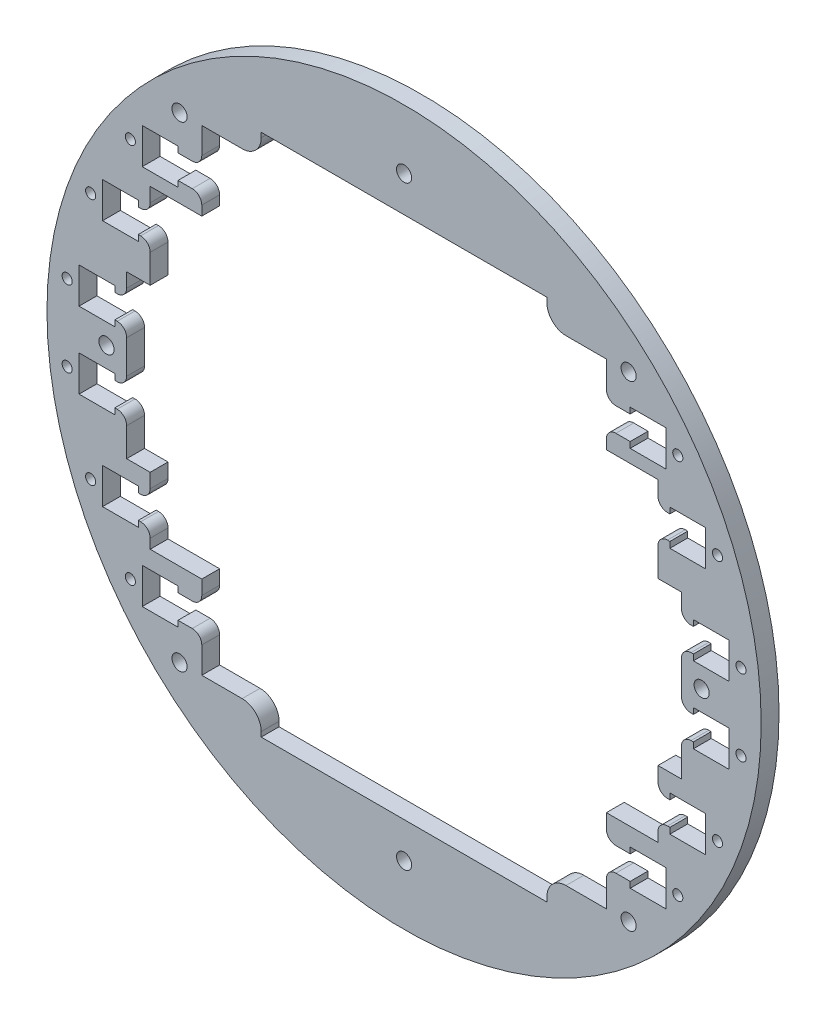
SolidWorks part; units mm, degrees
material "Delrin 2700 NC010, Low Viscosity Acetal Copolymer (SS)"
ref_plane "Front Plane" through (0, 0, 0) normal (0, 0, 1) x (1, 0, 0)
ref_plane "Top Plane" through (0, 0, 0) normal (0, 1, 0) x (1, 0, 0)
ref_plane "Right Plane" through (0, 0, 0) normal (1, 0, 0) x (0, 0, -1)
sketch "Sketch1" plane through (0, 0, 0) normal (0, 0, 1) x (1, 0, 0)
  circle A0 centre (0, 0) radius 95.25
  dimension "D1" = 190.5
extrude "Boss-Extrude1" add sketch "Sketch1" along normal blind 4.7625
sketch "Sketch11" plane through (0, 0, 4.7625) normal (0, 0, 1) x (1, 0, 0)
  line L0 (-69.8306, 55.5625) -> (-69.8306, 46.0375)
  line L1 (-69.8306, 46.0375) -> (-60.3056, 46.0375)
  line L2 (-60.3056, 46.0375) -> (-60.3056, 47.625)
  line L3 (-60.3056, 47.625) -> (-68.2431, 47.625)
  line L4 (-68.2431, 47.625) -> (-68.2431, 53.975)
  line L5 (-68.2431, 53.975) -> (-60.3056, 53.975)
  line L6 (-60.3056, 53.975) -> (-60.3056, 55.5625)
  line L7 (-60.3056, 55.5625) -> (-69.8306, 55.5625)
  line L8 (-69.8306, 50.8) -> (-65.0681, 50.8) construction
  line L9 (-86.6849, 14.9225) -> (-86.6849, 5.3975)
  line L10 (-86.6849, 5.3975) -> (-77.1599, 5.3975)
  line L11 (-77.1599, 5.3975) -> (-77.1599, 6.985)
  line L12 (-77.1599, 6.985) -> (-85.0974, 6.985)
  line L13 (-85.0974, 6.985) -> (-85.0974, 13.335)
  line L14 (-85.0974, 13.335) -> (-77.1599, 13.335)
  line L15 (-77.1599, 13.335) -> (-77.1599, 14.9225)
  line L16 (-77.1599, 14.9225) -> (-86.6849, 14.9225)
  line L17 (-80.4208, 37.7825) -> (-80.4208, 28.2575)
  line L18 (-80.4208, 28.2575) -> (-70.8958, 28.2575)
  line L19 (-70.8958, 28.2575) -> (-70.8958, 29.845)
  line L20 (-70.8958, 29.845) -> (-78.8333, 29.845)
  line L21 (-78.8333, 29.845) -> (-78.8333, 36.195)
  line L22 (-78.8333, 36.195) -> (-70.8958, 36.195)
  line L23 (-70.8958, 36.195) -> (-70.8958, 37.7825)
  line L24 (-70.8958, 37.7825) -> (-80.4208, 37.7825)
  line L25 (-80.4208, 33.02) -> (-75.6583, 33.02) construction
  line L26 (-86.6849, 10.16) -> (-81.9224, 10.16) construction
  line L27 (0, 0) -> (63.3649, 0) construction
  line L28 (-77.1599, -13.335) -> (-77.1599, -14.9225)
  line L29 (-77.1599, -14.9225) -> (-86.6849, -14.9225)
  line L30 (-85.0974, -13.335) -> (-77.1599, -13.335)
  line L31 (-86.6849, -14.9225) -> (-86.6849, -5.3975)
  line L32 (-85.0974, -6.985) -> (-85.0974, -13.335)
  line L33 (-77.1599, -6.985) -> (-85.0974, -6.985)
  line L34 (-77.1599, -5.3975) -> (-77.1599, -6.985)
  line L35 (-86.6849, -5.3975) -> (-77.1599, -5.3975)
  line L36 (-80.4208, -28.2575) -> (-70.8958, -28.2575)
  line L37 (-70.8958, -28.2575) -> (-70.8958, -29.845)
  line L38 (-70.8958, -29.845) -> (-78.8333, -29.845)
  line L39 (-80.4208, -37.7825) -> (-80.4208, -28.2575)
  line L40 (-78.8333, -29.845) -> (-78.8333, -36.195)
  line L41 (-70.8958, -37.7825) -> (-80.4208, -37.7825)
  line L42 (-78.8333, -36.195) -> (-70.8958, -36.195)
  line L43 (-70.8958, -36.195) -> (-70.8958, -37.7825)
  line L44 (-60.3056, -46.0375) -> (-60.3056, -47.625)
  line L45 (-60.3056, -47.625) -> (-68.2431, -47.625)
  line L46 (-69.8306, -46.0375) -> (-60.3056, -46.0375)
  line L47 (-69.8306, -55.5625) -> (-69.8306, -46.0375)
  line L48 (-68.2431, -47.625) -> (-68.2431, -53.975)
  line L49 (-68.2431, -53.975) -> (-60.3056, -53.975)
  line L50 (-60.3056, -55.5625) -> (-69.8306, -55.5625)
  line L51 (-60.3056, -53.975) -> (-60.3056, -55.5625)
  line L52 (0, 0) -> (0, 41.3514) construction
  line L53 (86.6849, 10.16) -> (81.9224, 10.16) construction
  line L54 (80.4208, 33.02) -> (75.6583, 33.02) construction
  line L55 (69.8306, 50.8) -> (65.0681, 50.8) construction
  line L56 (60.3056, -53.975) -> (60.3056, -55.5625)
  line L57 (60.3056, -55.5625) -> (69.8306, -55.5625)
  line L58 (68.2431, -53.975) -> (60.3056, -53.975)
  line L59 (68.2431, -47.625) -> (68.2431, -53.975)
  line L60 (69.8306, -55.5625) -> (69.8306, -46.0375)
  line L61 (69.8306, -46.0375) -> (60.3056, -46.0375)
  line L62 (60.3056, -47.625) -> (68.2431, -47.625)
  line L63 (60.3056, -46.0375) -> (60.3056, -47.625)
  line L64 (70.8958, -36.195) -> (70.8958, -37.7825)
  line L65 (78.8333, -36.195) -> (70.8958, -36.195)
  line L66 (70.8958, -37.7825) -> (80.4208, -37.7825)
  line L67 (78.8333, -29.845) -> (78.8333, -36.195)
  line L68 (80.4208, -37.7825) -> (80.4208, -28.2575)
  line L69 (70.8958, -29.845) -> (78.8333, -29.845)
  line L70 (70.8958, -28.2575) -> (70.8958, -29.845)
  line L71 (80.4208, -28.2575) -> (70.8958, -28.2575)
  line L72 (86.6849, -5.3975) -> (77.1599, -5.3975)
  line L73 (77.1599, -5.3975) -> (77.1599, -6.985)
  line L74 (77.1599, -6.985) -> (85.0974, -6.985)
  line L75 (85.0974, -6.985) -> (85.0974, -13.335)
  line L76 (86.6849, -14.9225) -> (86.6849, -5.3975)
  line L77 (85.0974, -13.335) -> (77.1599, -13.335)
  line L78 (77.1599, -14.9225) -> (86.6849, -14.9225)
  line L79 (77.1599, -13.335) -> (77.1599, -14.9225)
  line L80 (70.8958, 37.7825) -> (80.4208, 37.7825)
  line L81 (70.8958, 36.195) -> (70.8958, 37.7825)
  line L82 (78.8333, 36.195) -> (70.8958, 36.195)
  line L83 (78.8333, 29.845) -> (78.8333, 36.195)
  line L84 (70.8958, 29.845) -> (78.8333, 29.845)
  line L85 (70.8958, 28.2575) -> (70.8958, 29.845)
  line L86 (80.4208, 28.2575) -> (70.8958, 28.2575)
  line L87 (80.4208, 37.7825) -> (80.4208, 28.2575)
  line L88 (77.1599, 14.9225) -> (86.6849, 14.9225)
  line L89 (77.1599, 13.335) -> (77.1599, 14.9225)
  line L90 (85.0974, 13.335) -> (77.1599, 13.335)
  line L91 (85.0974, 6.985) -> (85.0974, 13.335)
  line L92 (77.1599, 6.985) -> (85.0974, 6.985)
  line L93 (77.1599, 5.3975) -> (77.1599, 6.985)
  line L94 (86.6849, 5.3975) -> (77.1599, 5.3975)
  line L95 (86.6849, 14.9225) -> (86.6849, 5.3975)
  line L96 (60.3056, 55.5625) -> (69.8306, 55.5625)
  line L97 (60.3056, 53.975) -> (60.3056, 55.5625)
  line L98 (68.2431, 53.975) -> (60.3056, 53.975)
  line L99 (68.2431, 47.625) -> (68.2431, 53.975)
  line L100 (60.3056, 47.625) -> (68.2431, 47.625)
  line L101 (60.3056, 46.0375) -> (60.3056, 47.625)
  line L102 (69.8306, 46.0375) -> (60.3056, 46.0375)
  line L103 (69.8306, 55.5625) -> (69.8306, 46.0375)
  circle A0 centre (0, 0) radius 82.55 construction
  point P14 (-65.0681, 55.5625)
  point P23 (-81.9224, 14.9225)
  point P32 (-75.6583, 37.7825)
  dimension "D1" = 165.1
  dimension "D2" = 9.525
  dimension "D3" = 9.525
  dimension "D4" = 1.5875
  dimension "D5" = 1.5875
  dimension "D6" = 1.5875
  dimension "D7" = 50.8
  dimension "D8" = 9.525
  dimension "D9" = 9.525
  dimension "D10" = 1.5875
  dimension "D11" = 1.5875
  dimension "D12" = 33.02
  dimension "D13" = 1.5875
  dimension "D14" = 9.525
  dimension "D15" = 9.525
  dimension "D16" = 1.5875
  dimension "D17" = 1.5875
  dimension "D18" = 1.5875
  dimension "D19" = 10.16
extrude "Cut-Extrude1" cut sketch "Sketch11" against normal through all
sketch "Sketch12" plane through (0, 0, 4.7625) normal (0, 0, 1) x (1, 0, 0)
  line L1 (-68.2431, 53.975) -> (68.2431, 53.975)
  line L2 (-68.2431, 53.975) -> (-68.2431, 47.625)
  line L3 (-68.2431, 47.625) -> (68.2431, 47.625)
  line L4 (68.2431, 53.975) -> (68.2431, 47.625)
  line L5 (-78.8333, 36.195) -> (78.8333, 36.195)
  line L6 (-78.8333, 36.195) -> (-78.8333, 29.845)
  line L7 (-78.8333, 29.845) -> (78.8333, 29.845)
  line L8 (78.8333, 36.195) -> (78.8333, 29.845)
  line L9 (-85.0974, 13.335) -> (85.0974, 13.335)
  line L10 (-85.0974, 13.335) -> (-85.0974, 6.985)
  line L11 (-85.0974, 6.985) -> (85.0974, 6.985)
  line L12 (85.0974, 13.335) -> (85.0974, 6.985)
  line L13 (-85.0974, -6.985) -> (85.0974, -6.985)
  line L14 (-85.0974, -6.985) -> (-85.0974, -13.335)
  line L15 (-85.0974, -13.335) -> (85.0974, -13.335)
  line L16 (85.0974, -6.985) -> (85.0974, -13.335)
  line L17 (-78.8333, -29.845) -> (78.8333, -29.845)
  line L18 (-78.8333, -29.845) -> (-78.8333, -36.195)
  line L19 (-78.8333, -36.195) -> (78.8333, -36.195)
  line L20 (78.8333, -29.845) -> (78.8333, -36.195)
  line L21 (-68.2431, -47.625) -> (68.2431, -47.625)
  line L22 (-68.2431, -47.625) -> (-68.2431, -53.975)
  line L23 (-68.2431, -53.975) -> (68.2431, -53.975)
  line L24 (68.2431, -47.625) -> (68.2431, -53.975)
extrude "Cut-Extrude2" cut sketch "Sketch12" against normal through all
sketch "Sketch13" plane through (0, 0, 4.7625) normal (0, 0, 1) x (1, 0, 0)
  line L0 (60.3056, 53.975) -> (-60.3056, 53.975) construction
  line L1 (53.9556, -63.5) -> (-53.9556, -63.5)
  line L2 (53.9556, -63.5) -> (53.9556, -41.275)
  line L3 (53.9556, 63.5) -> (-53.9556, 63.5)
  line L4 (-53.9556, -63.5) -> (-53.9556, -41.275)
  line L5 (53.9556, -63.5) -> (-53.9556, 63.5) construction
  line L6 (53.9556, 63.5) -> (-53.9556, -63.5) construction
  line L7 (-53.9556, 42.545) -> (-67.7208, 42.545)
  line L8 (-67.7208, -23.495) -> (-67.7208, -41.275)
  line L9 (-53.9556, -41.275) -> (-67.7208, -41.275)
  line L10 (-67.7208, 42.545) -> (-67.7208, 19.685)
  line L11 (-67.7208, 19.685) -> (-73.9849, 19.685)
  line L12 (0, 0) -> (0, 113.4572) construction
  line L13 (-67.7208, -23.495) -> (-73.9849, -23.495)
  line L14 (-73.9849, 19.685) -> (-73.9849, -23.495)
  line L15 (-60.3056, 53.975) -> (-60.3056, 55.5625) construction
  line L16 (-70.8958, 36.195) -> (-70.8958, 37.7825) construction
  line L17 (70.8958, 36.195) -> (-70.8958, 36.195) construction
  line L18 (77.1599, 13.335) -> (-77.1599, 13.335) construction
  line L19 (70.8958, -29.845) -> (-70.8958, -29.845) construction
  line L20 (-77.1599, 13.335) -> (-77.1599, 14.9225) construction
  line L21 (60.3056, -47.625) -> (-60.3056, -47.625) construction
  line L22 (-53.9556, 42.545) -> (-53.9556, 63.5)
  line L23 (53.9556, -41.275) -> (67.7208, -41.275)
  line L24 (53.9556, -63.5) -> (53.9556, -41.275)
  line L25 (67.7208, -23.495) -> (67.7208, -41.275)
  line L26 (67.7208, -23.495) -> (73.9849, -23.495)
  line L27 (73.9849, 19.685) -> (73.9849, -23.495)
  line L28 (67.7208, 19.685) -> (73.9849, 19.685)
  line L29 (67.7208, 42.545) -> (67.7208, 19.685)
  line L30 (53.9556, 42.545) -> (67.7208, 42.545)
  line L31 (53.9556, 42.545) -> (53.9556, 63.5)
  line L32 (53.9556, 42.545) -> (53.9556, 63.5)
  point P0 (0, 0)
  dimension "D1" = 9.525
  dimension "D2" = 6.35
  dimension "D3" = 3.175
  dimension "D4" = 6.35
  dimension "D5" = 6.35
  dimension "D6" = 6.35
  dimension "D7" = 3.175
  dimension "D8" = 6.35
extrude "Cut-Extrude3" cut sketch "Sketch13" against normal through all contours L30 L31 L3 L22 L7 L10 L11 L14 L13 L8 L9 L4 L1 L2 L23 L25 L26 L27 L28 L29
hole_wizard "#10-32 Tapped Hole1" positions "Sketch10" profile "Sketch9" tap size "#10-32" standard "ANSI Inch"
sketch "Sketch10" plane through (0, 0, 4.7625) normal (0, 0, 1) x (1, 0, 0)
  line L0 (-59.8919, 63.5) -> (59.8919, 63.5) construction
  point P0 (-59.8919, 63.5)
  point P2 (59.8919, 63.5)
  point P9 (0, 63.5)
  dimension "D1" = 63.5
  dimension "D2" = 119.7837
sketch "Sketch9" plane through (-59.8919, 63.5, 4.7625) normal (1, 0, 0) x (0, -1, 0)
  line L0 (0, 0) -> (0, 11.938)
  line L1 (0, 11.938) -> (2.0193, 11.938)
  line L2 (2.0193, 11.938) -> (2.0193, 0)
  line L5 (2.0193, 0) -> (0, 0)
  line L10 (0, 11.938) -> (-2.0193, 11.938) construction
  line L11 (0, -6.35) -> (0, 107.95) construction
  dimension "Tap Drill Dia." = 4.0386
  dimension "Tap Drill Depth" = 11.938
  dimension "Drill Angle" = 180
cosmetic thread "Hole Thread35" parameters "D1"=4.7625, "D2"=4.826
cosmetic thread "Hole Thread36" parameters "D1"=4.7625, "D2"=4.826
mirror "Mirror1" about plane through (0, 0, 0) normal (0, 1, 0) of "#10-32 Tapped Hole1"
sketch "Sketch14" plane through (0, 0, 4.7625) normal (0, 0, 1) x (1, 0, 0)
  line L1 (38.1, -69.85) -> (-38.1, -69.85)
  line L2 (38.1, -69.85) -> (38.1, 69.85)
  line L3 (38.1, 69.85) -> (-38.1, 69.85)
  line L4 (-38.1, -69.85) -> (-38.1, 69.85)
  line L5 (38.1, -69.85) -> (-38.1, 69.85) construction
  line L6 (38.1, 69.85) -> (-38.1, -69.85) construction
  point P0 (0, 0)
  dimension "D1" = 69.85
  dimension "D2" = 38.1
extrude "Cut-Extrude4" cut sketch "Sketch14" against normal through all
fillet "Fillet1" radius 5.08 4 edges at (38.1, -63.5, 2.3813) (-38.1, -63.5, 2.3813) (38.1, 63.5, 2.3813) (-38.1, 63.5, 2.3813)
fillet "Fillet3" radius 2.54 24 edges at (53.9556, 53.975, 2.3813) (53.9556, 47.625, 2.3813) (67.7208, 36.195, 2.3813) (67.7208, 29.845, 2.3813) (73.9849, 13.335, 2.3813) (73.9849, 6.985, 2.3813) (73.9849, -6.985, 2.3813) (73.9849, -13.335, 2.3813) (67.7208, -29.845, 2.3813) (67.7208, -36.195, 2.3813) (53.9556, -47.625, 2.3813) (53.9556, -53.975, 2.3813) (-53.9556, -53.975, 2.3813) (-53.9556, -47.625, 2.3813) (-67.7208, -36.195, 2.3813) (-67.7208, -29.845, 2.3813) (-73.9849, -13.335, 2.3813) (-73.9849, -6.985, 2.3813) (-73.9849, 6.985, 2.3813) (-73.9849, 13.335, 2.3813) (-67.7208, 29.845, 2.3813) (-67.7208, 36.195, 2.3813) (-53.9556, 47.625, 2.3813) (-53.9556, 53.975, 2.3813)
hole_wizard "#6-32 Tapped Hole1" positions "Sketch16" profile "Sketch15" tap size "#6-32" standard "ANSI Inch"
sketch "Sketch16" plane through (0, 0, 4.7625) normal (0, 0, 1) x (1, 0, 0)
  line L0 (-69.8306, 55.5625) -> (-69.8306, 46.0375) construction
  line L1 (-80.4208, 37.7825) -> (-80.4208, 28.2575) construction
  line L2 (-86.6849, 14.9225) -> (-86.6849, 5.3975) construction
  line L3 (-86.6849, -5.3975) -> (-86.6849, -14.9225) construction
  line L4 (-80.4208, -28.2575) -> (-80.4208, -37.7825) construction
  line L5 (-80.4208, -28.2575) -> (-80.4208, -37.7825) construction
  line L6 (-69.8306, -46.0375) -> (-69.8306, -55.5625) construction
  line L7 (0, 0) -> (0, 36.9166) construction
  point P0 (-73.0056, 50.8)
  point P5 (-69.8306, 50.8)
  point P16 (-80.4208, 33.02)
  point P17 (-83.5958, 33.02)
  point P19 (-89.8599, 10.16)
  point P21 (-89.8599, -10.16)
  point P23 (-83.5958, -33.02)
  point P25 (-73.0056, -50.8)
  point P31 (-86.6849, 10.16)
  point P34 (-86.6849, -10.16)
  point P37 (-80.4208, -33.02)
  point P44 (-69.8306, -50.8)
  point P50 (73.0056, -50.8)
  point P51 (83.5958, -33.02)
  point P52 (89.8599, -10.16)
  point P53 (89.8599, 10.16)
  point P54 (83.5958, 33.02)
  point P55 (73.0056, 50.8)
  dimension "D1" = 3.175
  dimension "D2" = 3.175
  dimension "D3" = 3.175
  dimension "D4" = 3.175
  dimension "D5" = 3.175
  dimension "D6" = 3.175
sketch "Sketch15" plane through (-73.0056, 50.8, 4.7625) normal (1, 0, 0) x (0, -1, 0)
  line L0 (0, 0) -> (0, 9.398)
  line L1 (0, 9.398) -> (1.3525, 9.398)
  line L2 (1.3525, 9.398) -> (1.3525, 0)
  line L5 (1.3525, 0) -> (0, 0)
  line L10 (0, 9.398) -> (-1.3525, 9.398) construction
  line L11 (0, -6.35) -> (0, 107.95) construction
  dimension "Tap Drill Dia." = 2.7051
  dimension "Tap Drill Depth" = 9.398
  dimension "Drill Angle" = 180
cosmetic thread "Hole Thread37" parameters "D1"=4.7625, "D2"=3.5052
cosmetic thread "Hole Thread38" parameters "D1"=4.7625, "D2"=3.5052
cosmetic thread "Hole Thread39" parameters "D1"=4.7625, "D2"=3.5052
cosmetic thread "Hole Thread40" parameters "D1"=4.7625, "D2"=3.5052
cosmetic thread "Hole Thread41" parameters "D1"=4.7625, "D2"=3.5052
cosmetic thread "Hole Thread42" parameters "D1"=4.7625, "D2"=3.5052
cosmetic thread "Hole Thread43" parameters "D1"=4.7625, "D2"=3.5052
cosmetic thread "Hole Thread44" parameters "D1"=4.7625, "D2"=3.5052
cosmetic thread "Hole Thread45" parameters "D1"=4.7625, "D2"=3.5052
cosmetic thread "Hole Thread46" parameters "D1"=4.7625, "D2"=3.5052
cosmetic thread "Hole Thread47" parameters "D1"=4.7625, "D2"=3.5052
cosmetic thread "Hole Thread48" parameters "D1"=4.7625, "D2"=3.5052
hole_wizard "#10-32 Tapped Hole3" positions "Sketch18" profile "Sketch19" tap size "#10-32" standard "ANSI Inch" end condition through all
sketch "Sketch18" plane through (0, 0, 4.7625) normal (0, 0, 1) x (1, 0, 0)
  circle A0 centre (0, 0) radius 79.375
  point P8 (0, 79.375)
  point P10 (-79.375, 0)
  point P12 (0, -79.375)
  point P14 (79.375, 0)
  dimension "D1" = 158.75
sketch "Sketch19" plane through (0, 79.375, 4.7625) normal (1, 0, 0) x (0, -1, 0)
  line L0 (0, 0) -> (0, 4.7625)
  line L1 (0, 4.7625) -> (2.0193, 4.7625)
  line L2 (2.0193, 4.7625) -> (2.0193, 0)
  line L5 (2.0193, 0) -> (0, 0)
  line L11 (0, -6.35) -> (0, 107.95) construction
  dimension "Thru Tap Drill Dia." = 4.0386
  dimension "Thru Tap Drill Depth" = 4.7625
cosmetic thread "Hole Thread49" parameters "D2"=4.826
cosmetic thread "Hole Thread50" parameters "D2"=4.826
cosmetic thread "Hole Thread51" parameters "D2"=4.826
cosmetic thread "Hole Thread52" parameters "D2"=4.826
